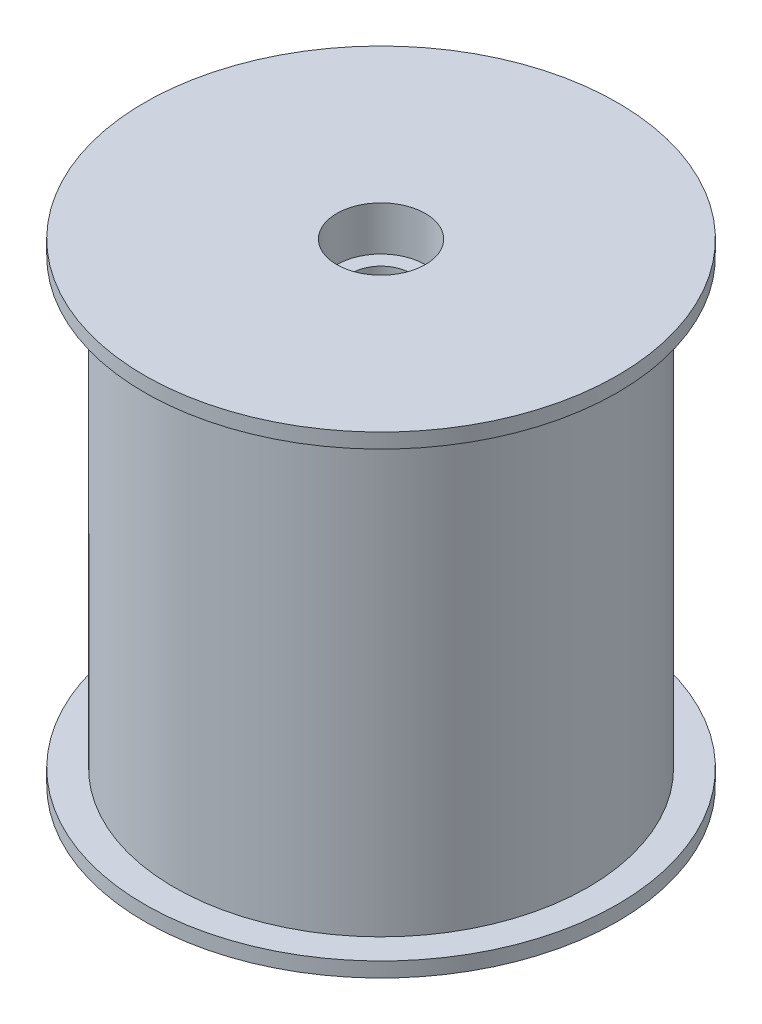
SolidWorks part; units mm, degrees
ref_plane "Front Plane" through (0, 0, 0) normal (0, 0, 1) x (1, 0, 0)
ref_plane "Top Plane" through (0, 0, 0) normal (0, 1, 0) x (1, 0, 0)
ref_plane "Right Plane" through (0, 0, 0) normal (1, 0, 0) x (0, 0, -1)
sketch "Sketch1" plane through (0, 0, 0) normal (0, 0, 1) x (1, 0, 0)
  line L0 (0, 0) -> (0, 10.5079) construction
  line L1 (1.5, 13.5079) -> (8, 13.5079)
  line L2 (8, 13.5079) -> (8, 13.0079)
  line L3 (8, 13.0079) -> (7, 13.0079)
  line L4 (7, 13.0079) -> (7, -1.9921)
  line L5 (7, -1.9921) -> (8, -1.9921)
  line L6 (8, -1.9921) -> (8, -2.4921)
  line L7 (8, -2.4921) -> (3.75, -2.4921)
  line L8 (3.75, -2.4921) -> (3.75, 10.5079)
  line L9 (3.75, 10.5079) -> (1, 10.5079)
  line L11 (1.5, 13.5079) -> (1.5, 12.0079)
  line L12 (1.5, 12.0079) -> (1, 12.0079)
  line L13 (1, 12.0079) -> (1, 10.5079)
  line L14 (0, 13.5079) -> (0, 21.898) construction
  dimension "D1" = 14
  dimension "D2" = 1
  dimension "D3" = 0.5
  dimension "D4" = 3
  dimension "D5" = 15
  dimension "D6" = 7.5
  dimension "D7" = 3
  dimension "D8" = 2
  dimension "D9" = 1.5
revolve "Revolve1" add sketch "Sketch1" angle 360 about L0
